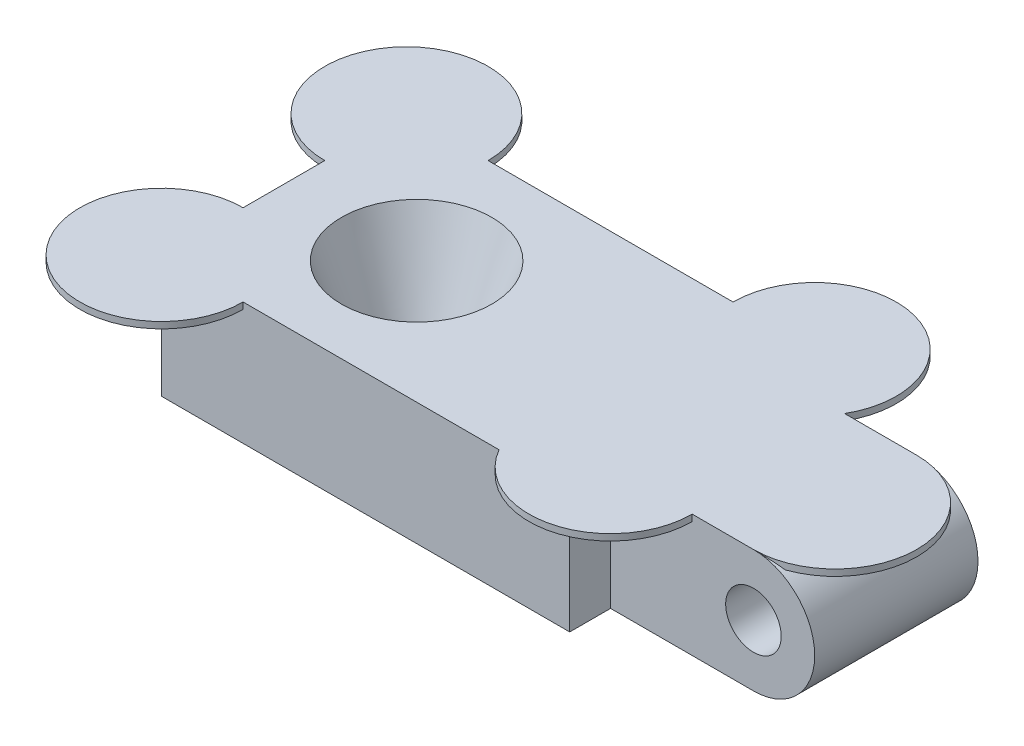
SolidWorks part; units mm, degrees
ref_plane "Front Plane" through (0, 0, 0) normal (0, 0, 1) x (1, 0, 0)
ref_plane "Top Plane" through (0, 0, 0) normal (0, 1, 0) x (1, 0, 0)
ref_plane "Right Plane" through (0, 0, 0) normal (1, 0, 0) x (0, 0, -1)
sketch "Sketch1" plane through (0, 0, 0) normal (0, 0, 1) x (1, 0, 0)
  line L1 (-17.145, -3.81) -> (17.145, -3.81)
  line L2 (-17.145, -3.81) -> (-17.145, 3.81)
  line L3 (-17.145, 3.81) -> (17.145, 3.81)
  line L4 (17.145, -3.81) -> (17.145, 3.81) construction
  line L5 (-17.145, -3.81) -> (17.145, 3.81) construction
  line L6 (-17.145, 3.81) -> (17.145, -3.81) construction
  arc A0 (17.145, 3.81) -> (17.145, -3.81) centre (17.145, 0) cw
  point P0 (0, 0)
  dimension "D1" = 7.62
  dimension "D2" = 34.29
extrude "Boss-Extrude1" add sketch "Sketch1" along normal blind 10.16
hole_wizard "#4 Clearance Hole1" positions "Sketch3" profile "Sketch2" hole size "#4" standard "ANSI Inch" end condition through all
sketch "Sketch3" plane through (0, 0, 10.16) normal (0, 0, 1) x (1, 0, 0)
  point P0 (17.145, 0)
sketch "Sketch2" plane through (17.145, 0, 10.16) normal (1, 0, 0) x (0, -1, 0)
  line L0 (0, 0) -> (0, 10.16)
  line L1 (0, 10.16) -> (1.7272, 10.16)
  line L2 (1.7272, 10.16) -> (1.7272, 0)
  line L5 (1.7272, 0) -> (0, 0)
  line L11 (0, -6.35) -> (0, 107.95) construction
  dimension "Thru Hole Dia." = 3.4544
  dimension "Thru Hole Depth" = 10.16
sketch "Sketch4" plane through (0, -3.81, 0) normal (0, 1, 0) x (1, 0, 0)
  line L0 (-17.145, -10.16) -> (-17.145, 0) construction
  circle A0 centre (-8.89, -5.08) radius 1.905
  point P0 (-8.89, -5.08)
  dimension "D2" = 3.81
  dimension "D1" = 8.255
extrude "Cut-Extrude1" cut sketch "Sketch4" along normal through all draft 20 draft outward yes
sketch "Sketch5" plane through (0, -3.81, 0) normal (0, -1, 0) x (1, 0, 0)
  circle A0 centre (-8.89, 5.08) radius 4.1275
  dimension "D1" = 8.255
extrude "Cut-Extrude2" cut sketch "Sketch5" against normal blind 1.27
sketch "Sketch6" plane through (0, -3.81, 0) normal (0, -1, 0) x (1, 0, 0)
  line L0 (-17.145, 5.08) -> (20.955, 5.08) construction
  line L1 (-17.145, 10.16) -> (8.255, 10.16)
  line L2 (-17.145, 10.16) -> (-17.145, 12.7)
  line L3 (-17.145, 12.7) -> (8.255, 12.7)
  line L4 (8.255, 10.16) -> (8.255, 12.7)
  line L5 (-17.145, 10.16) -> (-17.145, 0) construction
  line L6 (20.955, 0) -> (20.955, 10.16) construction
  line L7 (8.255, 0) -> (8.255, -2.54)
  line L8 (-17.145, -2.54) -> (8.255, -2.54)
  line L9 (-17.145, 0) -> (-17.145, -2.54)
  line L10 (-17.145, 0) -> (8.255, 0)
  dimension "D1" = 2.54
  dimension "D2" = 25.4
extrude "Boss-Extrude2" add sketch "Sketch6" against normal through all
sketch "Sketch7" plane through (0, 3.81, 0) normal (0, 1, 0) x (1, 0, 0)
  line L1 (-17.145, 2.54) -> (8.255, 2.54) construction
  line L2 (17.145, -10.16) -> (17.145, 0) construction
  circle A0 centre (8.255, 2.54) radius 5.08
  circle A1 centre (-17.145, -12.7) radius 5.08
  circle A2 centre (-17.145, 2.54) radius 5.08
  circle A3 centre (8.255, -10.16) radius 5.08
  circle A4 centre (17.145, -5.08) radius 5.08
  dimension "D1" = 10.16
  dimension "D2" = 10.16
  dimension "D3" = 10.16
  dimension "D4" = 10.16
  dimension "D5" = 10.16
extrude "PrintTabs" add sketch "Sketch7" against normal blind 0.4
